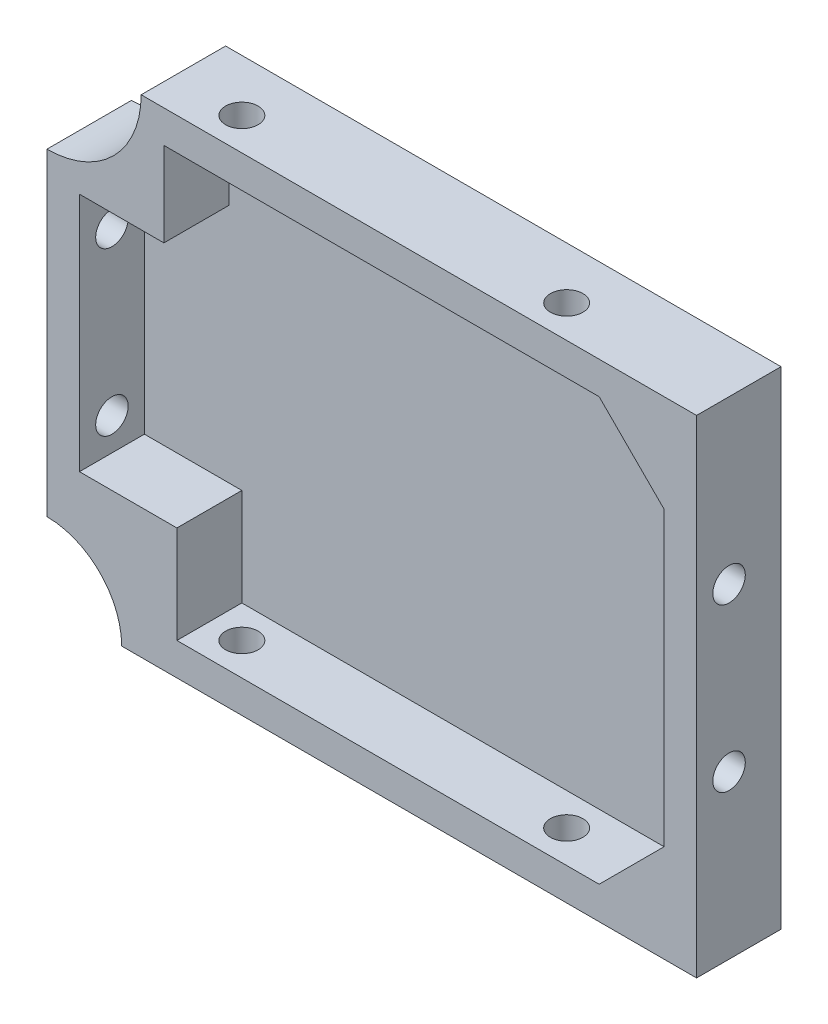
SolidWorks part; units mm, degrees
ref_plane "Plan de face" through (0, 0, 0) normal (0, 0, 1) x (1, 0, 0)
ref_plane "Plan de dessus" through (0, 0, 0) normal (0, 1, 0) x (1, 0, 0)
ref_plane "Plan de droite" through (0, 0, 0) normal (1, 0, 0) x (0, 0, -1)
sketch "Esquisse1" plane through (0, 0, 0) normal (0, 0, 1) x (1, 0, 0)
  line L0 (44.1184, 33.7284) -> (54.1184, 33.7284)
  line L1 (-45.8816, 33.7284) -> (44.1184, 33.7284)
  line L2 (-45.8816, 33.7284) -> (-45.8816, -41.2716)
  line L3 (-45.8816, -41.2716) -> (54.1184, -41.2716)
  line L4 (54.1184, 23.7284) -> (54.1184, -41.2716)
  line L5 (54.1184, 33.7284) -> (54.1184, 23.7284)
  point P6 (54.1184, 33.7284)
  dimension "D1" = 100
  dimension "D2" = 75
extrude "Boss.-Extru.1" add sketch "Esquisse1" along normal blind 13
shell "Coque1" thickness 5
sketch "Esquisse2" plane through (-45.8816, 0, 0) normal (-1, 0, 0) x (0, 0, 1)
  line L0 (13, 33.7284) -> (13, -41.2716) construction
  line L1 (13, 33.7284) -> (0, 33.7284) construction
  line L2 (13, -41.2716) -> (0, -41.2716) construction
  circle A0 centre (8, 8.7284) radius 2.5
  circle A1 centre (8, -16.2716) radius 2.5
  dimension "D1" = 5
  dimension "D2" = 5
  dimension "D3" = 5
  dimension "D4" = 5
  dimension "D5" = 25
  dimension "D6" = 25
extrude "Enlèv. mat.-Extru.1" cut sketch "Esquisse2" against normal up to surface (100 mm away) contours A1 | A0 up to face at (54.1184, -3.7716, 6.5)
sketch "Esquisse3" plane through (0, -41.2716, 0) normal (0, -1, 0) x (1, 0, 0)
  line L0 (-45.8816, 13) -> (54.1184, 13) construction
  line L2 (54.1184, 13) -> (54.1184, 0) construction
  line L3 (-45.8816, 13) -> (-45.8816, 0) construction
  circle A0 centre (-20.8816, 8) radius 2.5
  circle A1 centre (29.1184, 8) radius 2.5
  dimension "D1" = 5
  dimension "D2" = 5
  dimension "D3" = 5
  dimension "D4" = 5
  dimension "D5" = 25
  dimension "D6" = 25
extrude "Enlèv. mat.-Extru.2" cut sketch "Esquisse3" against normal up to surface (75 mm away) up to face at (4.1184, 33.7284, 6.5)
sketch "Esquisse4" plane through (0, 0, 3) normal (0, 0, 1) x (1, 0, 0)
  line L1 (49.1184, 28.7284) -> (-40.8816, 28.7284) construction
  line L2 (-40.8816, 28.7284) -> (-40.8816, -36.2716) construction
  line L3 (-45.8816, 33.7284) -> (-27.8816, 33.7284)
  line L4 (-45.8816, 33.7284) -> (-45.8816, 15.7284)
  line L5 (49.1184, 28.7284) -> (49.1184, 18.7284)
  line L6 (49.1184, -36.2716) -> (49.1184, 28.7284) construction
  line L7 (49.1184, 18.7284) -> (39.1184, 28.7284)
  line L8 (39.1184, 28.7284) -> (49.1184, 28.7284)
  line L9 (49.1184, 28.7284) -> (-40.8816, 28.7284) construction
  line L10 (49.1184, -36.2716) -> (49.1184, -26.2716)
  line L11 (49.1184, -26.2716) -> (39.1184, -36.2716)
  line L12 (-40.8816, -36.2716) -> (49.1184, -36.2716) construction
  line L13 (39.1184, -36.2716) -> (49.1184, -36.2716)
  line L14 (-40.8816, -21.2716) -> (-25.8816, -21.2716)
  line L15 (-45.8816, 15.7284) -> (-27.8816, 15.7284)
  line L16 (-40.8816, 28.7284) -> (-40.8816, -36.2716) construction
  line L17 (-25.8816, -21.2716) -> (-25.8816, -36.2716)
  line L18 (-25.8816, -36.2716) -> (-40.8816, -36.2716)
  line L19 (-40.8816, -36.2716) -> (-40.8816, -21.2716)
  line L20 (-27.8816, 33.7284) -> (-27.8816, 15.7284)
  dimension "D1" = 18
  dimension "D2" = 18
  dimension "D3" = 10
  dimension "D4" = 10
  dimension "D5" = 10
  dimension "D6" = 10
  dimension "D7" = 15
  dimension "D8" = 15
extrude "Boss.-Extru.2" add sketch "Esquisse4" along normal up to surface (10 mm away) up to face at (4.1184, -3.7716, 13)
sketch "Esquisse6" plane through (0, 0, 13) normal (0, 0, 1) x (1, 0, 0)
  circle A0 centre (-45.8816, -41.2716) radius 11.5
  circle A1 centre (-45.8816, 33.7284) radius 14.5
  dimension "D1" = 23
  dimension "D2" = 29
extrude "Enlèv. mat.-Extru.4" cut sketch "Esquisse6" against normal up to surface (13 mm away) up to face at (4.1184, -3.7716, 0)
